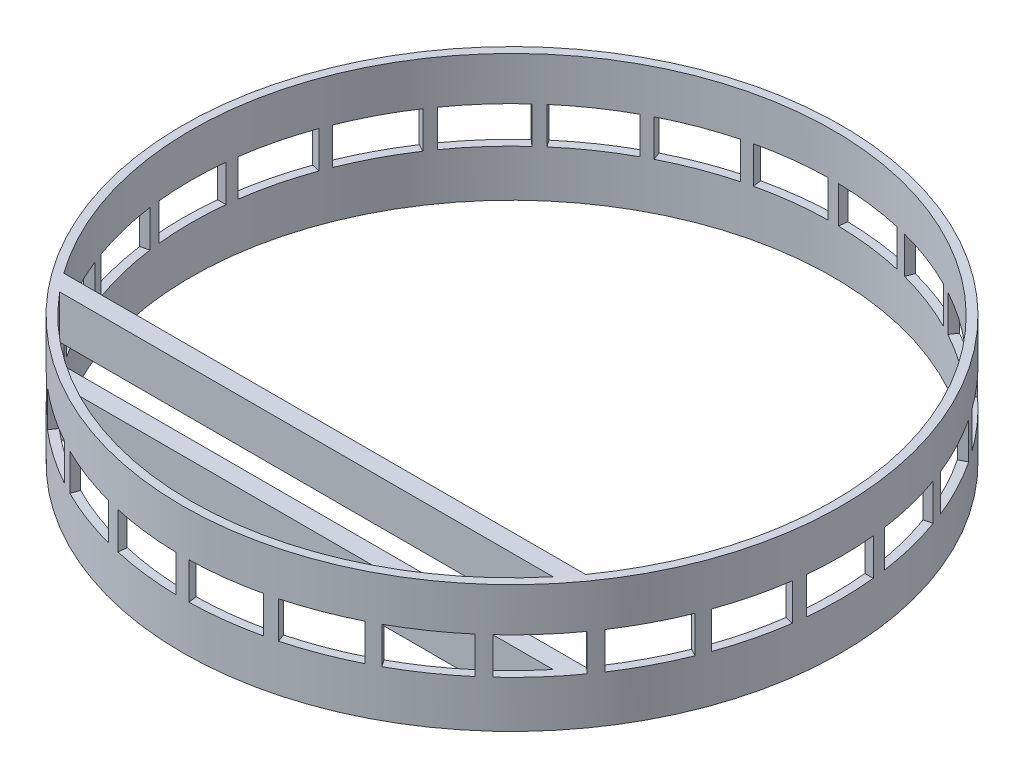
SolidWorks part; units mm, degrees
material "ABS PC"
ref_plane "Front" through (0, 0, 0) normal (0, 0, 1) x (1, 0, 0)
ref_plane "Top" through (0, 0, 0) normal (0, 1, 0) x (1, 0, 0)
ref_plane "Right" through (0, 0, 0) normal (1, 0, 0) x (0, 0, -1)
ref_plane "Plane2" through (0, 0, 56) normal (0, 0, 1) x (1, 0, 0)
sketch "Sketch1" plane through (0, 0, 0) normal (0, 1, 0) x (1, 0, 0)
  line L0 (81.0324, -56) -> (-81.0324, -56) construction
  line L1 (81.0324, -56) -> (77.9744, -56)
  line L2 (-50, -56) -> (50, -56) construction
  line L3 (-77.9744, -56) -> (-81.0324, -56)
  line L4 (76.9735, -61.46) -> (-76.9735, -61.46)
  circle A0 centre (0, 0) radius 96
  circle A1 centre (0, 0) radius 98.5
  dimension "D1" = 197
  dimension "D2" = 192
  dimension "D3" = 5.46
extrude "Boss-Extrude1" add sketch "Sketch1" along normal blind 38 contours L4 A1 L1 A0 | A0 L0 L4 | L3 A1 L4 A0 | L1 A1 L3 A0 | L4 A1 A0
sketch "Sketch2" plane through (0, 0, 0) normal (1, 0, 0) x (0, 0, -1)
  line L0 (-56, 0) -> (96, 0) construction
  line L1 (-10, 25) -> (10, 25)
  line L2 (-10, 25) -> (-10, 14)
  line L3 (-10, 14) -> (10, 14)
  line L4 (10, 25) -> (10, 14)
  line L7 (0, 0) -> (0, 25) construction
  dimension "D2" = 11
  dimension "D3" = 20
  dimension "D4" = 14
extrude "Cut-Extrude1" cut sketch "Sketch2" against normal through all
pattern_circular "CirPattern1" count 26 over 360 about axis through (0, 0, 0) along (0, 1, 0) of "Cut-Extrude1"
